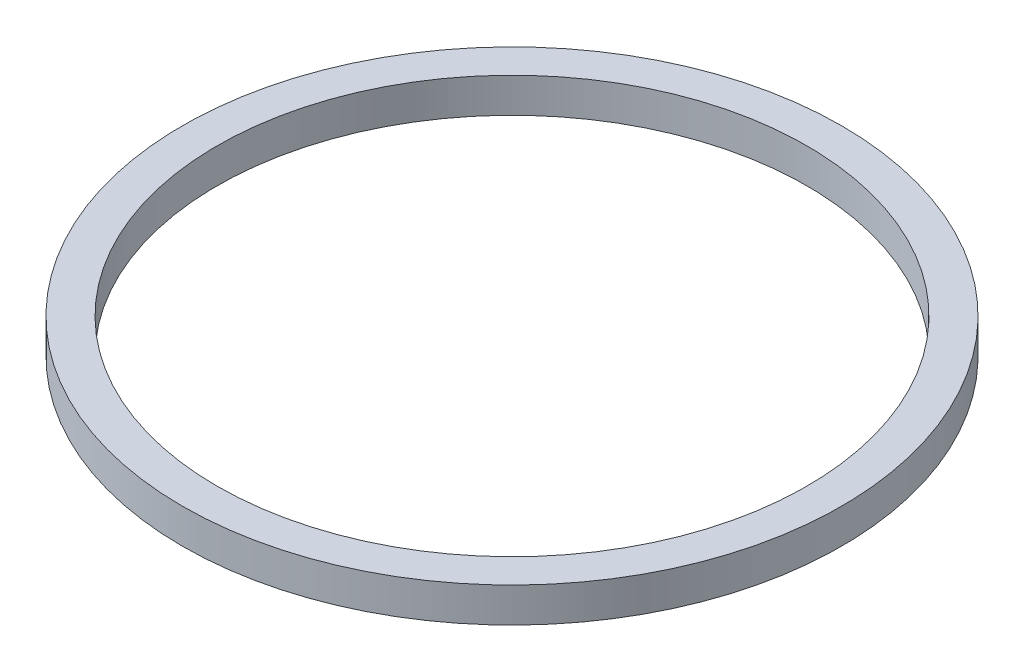
SolidWorks part; units mm, degrees
ref_plane "Front Plane" through (0, 0, 0) normal (0, 0, 1) x (1, 0, 0)
ref_plane "Top Plane" through (0, 0, 0) normal (0, 1, 0) x (1, 0, 0)
ref_plane "Right Plane" through (0, 0, 0) normal (1, 0, 0) x (0, 0, -1)
sketch "Sketch2" plane through (0, 0, 0) normal (0, 1, 0) x (1, 0, 0)
  circle A0 centre (0, 0) radius 8.5
  circle A1 centre (0, 0) radius 9.5
  dimension "D1" = 17
  dimension "D2" = 19
extrude "Boss-Extrude1" add sketch "Sketch2" along normal blind 1
